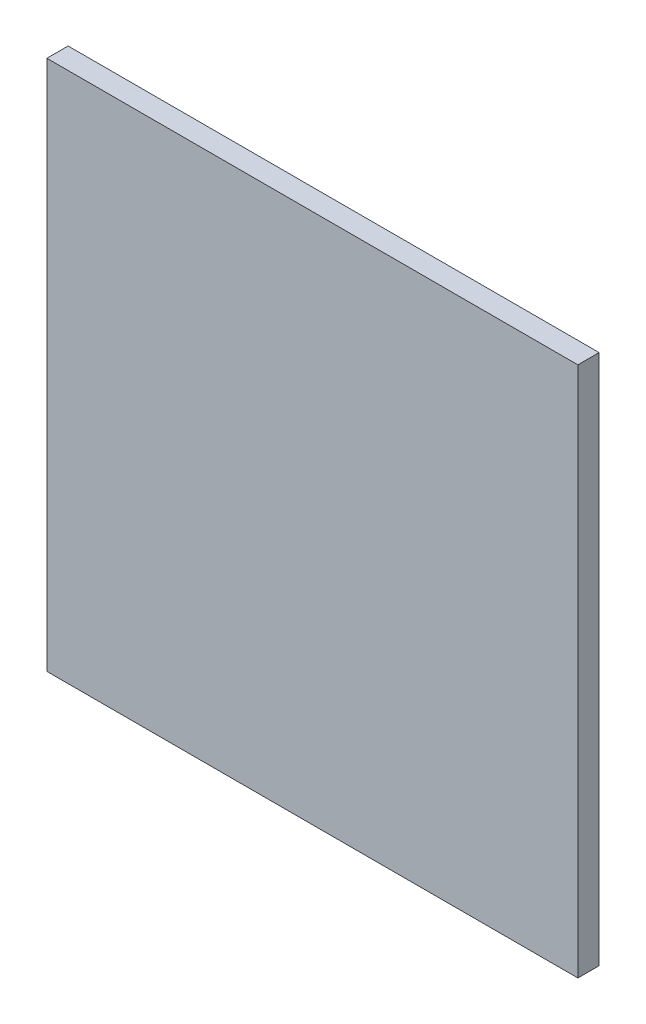
SolidWorks part; units mm, degrees
ref_plane "前视基准面" through (0, 0, 0) normal (0, 0, 1) x (1, 0, 0)
ref_plane "上视基准面" through (0, 0, 0) normal (0, 1, 0) x (1, 0, 0)
ref_plane "右视基准面" through (0, 0, 0) normal (1, 0, 0) x (0, 0, -1)
sketch "草图1" plane through (0, 0, 0) normal (0, 0, 1) x (1, 0, 0)
  line L1 (-108.2731, 75.9494) -> (141.7269, 75.9494)
  line L2 (-108.2731, 75.9494) -> (-108.2731, -174.0506)
  line L3 (-108.2731, -174.0506) -> (141.7269, -174.0506)
  line L4 (141.7269, 75.9494) -> (141.7269, -174.0506)
  dimension "D1" = 250
  dimension "D2" = 250
extrude "凸台-拉伸1" add sketch "草图1" along normal blind 10 contours L1 L4 L3 L2
sketch "草图4" plane through (0, 0, 0) normal (0, 0, -1) x (-1, 0, 0)
  circle A0 centre (-24.4794, -68.7942) radius 8
  dimension "D1" = 16
extrude "凸台-拉伸2" add sketch "草图4" along normal blind 4 contours A0
sketch "草图6" plane through (0, 0, 0) normal (0, 0, -1) x (-1, 0, 0)
  circle A0 centre (-128.9942, 14.3874) radius 1.5
  dimension "D1" = 3
extrude "凸台-拉伸3" add sketch "草图6" along normal blind 3 contours A0
pattern_linear "阵列(线性)1" count 6 spacing 30 along (0, -1, 0) of "凸台-拉伸3"
draft "拔模1" type of draft neutral plane draft angle 30 faces to draft 1 face at (127.4942, 14.3874, -3) neutral plane through (128.9942, 14.3874, -3) neutral plane normal (0, 0, -1) parameters "D1"=30
pattern_linear "阵列(线性)2" count 6 spacing 30 along (0, -1, 0) of "凸台-拉伸3"
draft "拔模2" type of draft neutral plane draft angle 30 faces to draft 1 face at (127.4942, -15.6126, -3) neutral plane through (128.9942, -15.6126, -3) neutral plane normal (0, 0, -1) parameters "D1"=30
draft "拔模3" type of draft neutral plane draft angle 30 faces to draft 1 face at (127.4942, -45.6126, -3) neutral plane through (128.9942, -45.6126, -3) neutral plane normal (0, 0, -1) parameters "D1"=30
draft "拔模4" type of draft neutral plane draft angle 30 faces to draft 1 face at (127.4942, -75.6126, -3) neutral plane through (128.9942, -75.6126, -3) neutral plane normal (0, 0, -1) parameters "D1"=30
draft "拔模5" type of draft neutral plane draft angle 30 faces to draft 1 face at (127.4942, -105.6126, -3) neutral plane through (128.9942, -105.6126, -3) neutral plane normal (0, 0, -1) parameters "D1"=30
draft "拔模6" type of draft neutral plane draft angle 30 faces to draft 1 face at (127.4942, -135.6126, -3) neutral plane through (128.9942, -135.6126, -3) neutral plane normal (0, 0, -1) parameters "D1"=30
